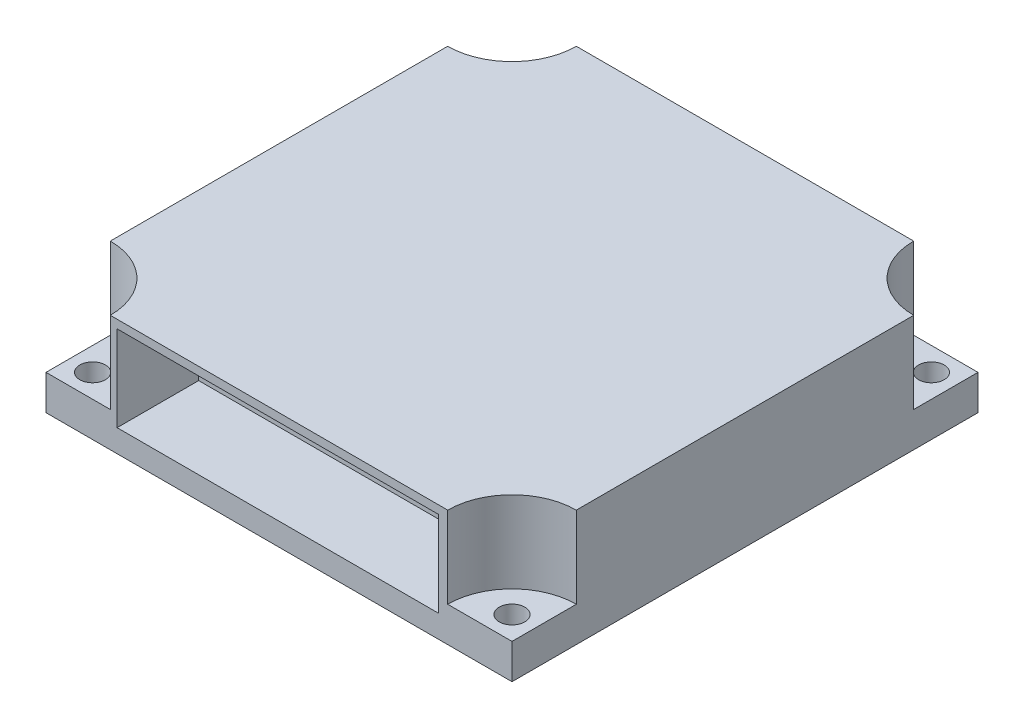
SolidWorks part; units mm, degrees
ref_plane "Front Plane" through (0, 0, 0) normal (0, 0, 1) x (1, 0, 0)
ref_plane "Top Plane" through (0, 0, 0) normal (0, 1, 0) x (1, 0, 0)
ref_plane "Right Plane" through (0, 0, 0) normal (1, 0, 0) x (0, 0, -1)
sketch "Sketch1" plane through (0, 0, 0) normal (0, 1, 0) x (1, 0, 0)
  line L1 (0, 0) -> (40, 0)
  line L2 (0, 0) -> (0, 40)
  line L3 (0, 40) -> (40, 40)
  line L4 (40, 0) -> (40, 40)
  circle A0 centre (2, 38) radius 1.1
  circle A1 centre (38, 38) radius 1.1
  circle A2 centre (2, 2) radius 1.1
  circle A3 centre (38, 2) radius 1.1
  dimension "D3" = 2.2
  dimension "D4" = 2.2
  dimension "D5" = 2.2
  dimension "D6" = 2.2
  dimension "D1" = 40
  dimension "D2" = 40
  dimension "D7" = 36
  dimension "D8" = 36
  dimension "D9" = 36
  dimension "D10" = 36
  dimension "D11" = 0
  dimension "D12" = 0
  dimension "D13" = 2
  dimension "D14" = 2
extrude "Boss-Extrude1" add sketch "Sketch1" along normal blind 10
sketch "Sketch2" plane through (0, 10, 0) normal (0, 1, 0) x (1, 0, 0)
  line L0 (40, 40) -> (0, 40) construction
  line L1 (0, 0) -> (40, 0) construction
  line L4 (40, 0) -> (40, 40) construction
  line L6 (0, 40) -> (0, 0) construction
  line L7 (0, 0) -> (5.5193, 0)
  line L8 (40, 0) -> (40, 5.5193)
  line L9 (40, 40) -> (34.4807, 40)
  line L10 (0, 40) -> (0, 34.4807)
  line L11 (0, 5.5193) -> (0, 0)
  line L12 (5.5193, 40) -> (0, 40)
  line L13 (34.4807, 0) -> (40, 0)
  line L14 (40, 34.4807) -> (40, 40)
  arc A0 (5.5193, 40) -> (0, 34.4807) centre (0, 40) cw
  arc A1 (40, 34.4807) -> (34.4807, 40) centre (40, 40) cw
  arc A2 (34.4807, 0) -> (40, 5.5193) centre (40, 0) cw
  arc A3 (0, 5.5193) -> (5.5193, 0) centre (0, 0) cw
  dimension "D1" = 4
extrude "Cut-Extrude1" cut sketch "Sketch2" against normal blind 7
sketch "Sketch3" plane through (0, 0, 0) normal (0, 0, 1) x (1, 0, 0)
  line L1 (6.1041, 9.2867) -> (33.6753, 9.2867)
  line L2 (6.1041, 9.2867) -> (6.1041, 1.9388)
  line L3 (6.1041, 1.9388) -> (33.6753, 1.9388)
  line L4 (33.6753, 9.2867) -> (33.6753, 1.9388)
extrude "Cut-Extrude2" cut sketch "Sketch3" against normal blind 7
equation "\"D4@Sketch1\"=\"D3@Sketch1\""
equation "\"D5@Sketch1\"=\"D3@Sketch1\""
equation "\"D6@Sketch1\"=\"D3@Sketch1\""
